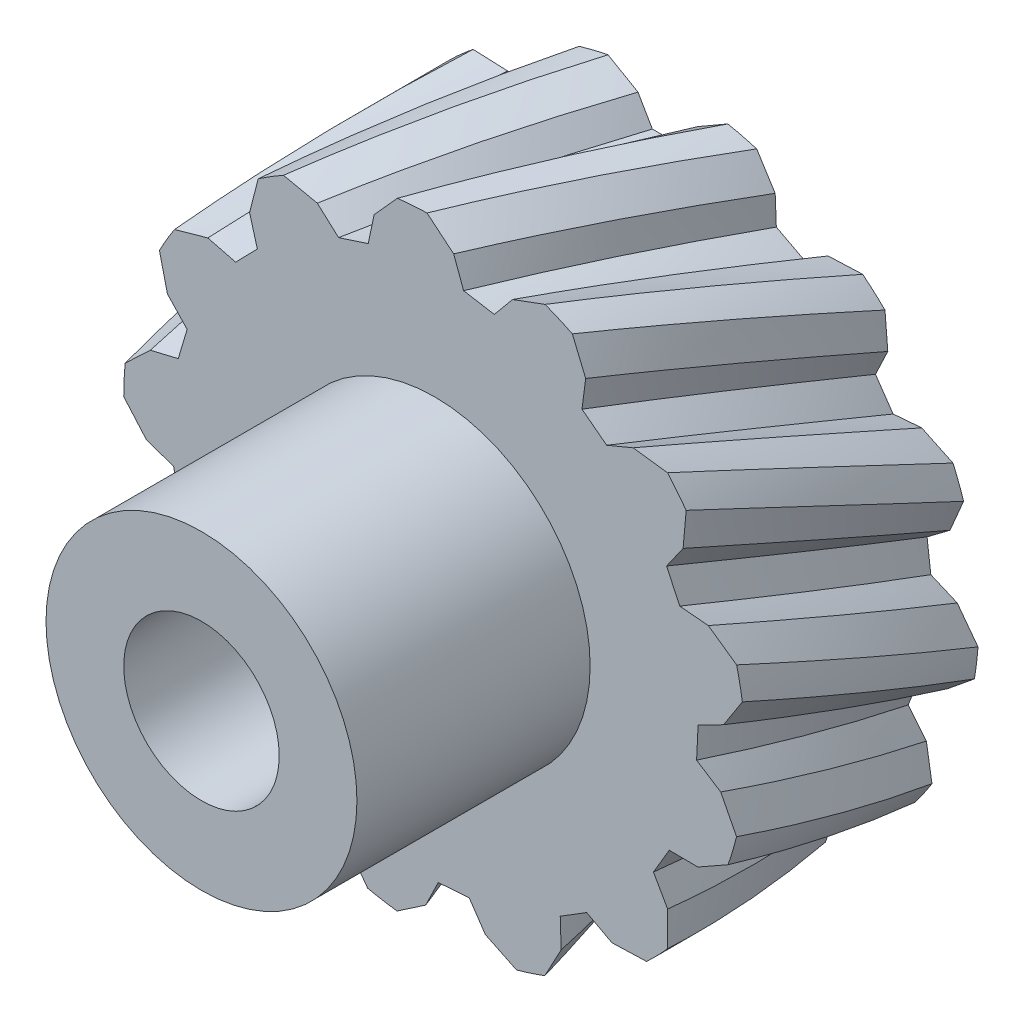
SolidWorks part; units mm, degrees
ref_plane "Ön Düzlem" through (0, 0, 0) normal (0, 0, 1) x (1, 0, 0)
ref_plane "Üst Düzlem" through (0, 0, 0) normal (0, 1, 0) x (1, 0, 0)
ref_plane "Sağ Düzlem" through (0, 0, 0) normal (1, 0, 0) x (0, 0, -1)
sketch "Çizim1" plane through (0, 0, 0) normal (0, 0, 1) x (1, 0, 0)
  circle A0 centre (0, 0) radius 20
  dimension "D1" = 40
extrude "Yükseklik-Ekstrüzyon1" add sketch "Çizim1" along normal blind 30
sketch "Çizim2" plane through (0, 0, 30) normal (0, 0, 1) x (1, 0, 0)
  circle A0 centre (0, 0) radius 20
  circle A1 centre (0, 0) radius 10
  dimension "D1" = 40
  dimension "D2" = 20
extrude "Kes-Ekstrüzyon2" cut sketch "Çizim2" against normal blind 15
sketch "Çizim3" plane through (0, 0, 30) normal (0, 0, 1) x (1, 0, 0)
  circle A0 centre (0, 0) radius 5
  dimension "D1" = 10
extrude "Kes-Ekstrüzyon3" cut sketch "Çizim3" against normal blind 40
sketch "Çizim5" plane through (0, 0, 0) normal (0, 0, -1) x (-1, 0, 0)
  circle A0 centre (0, 0) radius 20
curve "Helis/Spiral1" pitch 300 height 15 turns 0.05
sketch "Çizim6" plane through (0, 0, 0) normal (0, 0, -1) x (-1, 0, 0)
  line L0 (0, 20) -> (0, 16.9146) construction
  line L1 (-1, 16.9146) -> (1, 16.9146)
  line L2 (1, 16.9146) -> (1.9224, 18.5123)
  line L3 (-1, 16.9146) -> (-1.9224, 18.5123)
  line L4 (1.9224, 18.5123) -> (4.7668, 20.1545)
  line L5 (-1.9224, 18.5123) -> (-4.7668, 20.1545)
  line L6 (4.7668, 20.1545) -> (-4.7668, 20.1545)
  circle A0 centre (0, 0) radius 20 construction
  spline S0 degree 3 poles (0, 20) (0.6981, 20) (2.0944, 19.9268) (4.1658, 19.5987) (5.5164, 19.2369) (6.1803, 19.0211) knots 0 0 0 0 0.333333 0.666667 1 1 1 1 construction
  dimension "D1" = 2
  dimension "D2" = 120
sweep "Kes-Süpür2" cut profiles "Çizim6" path "Helis/Spiral1"
pattern_circular "Dairesel Kaplama1" count 13 over 360 about axis through (0, 0, 0) along (0, 0, 1) of "Kes-Süpür2"
